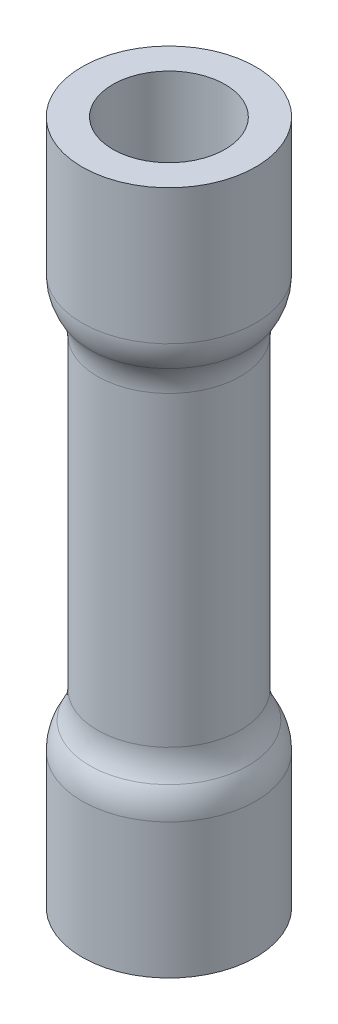
SolidWorks part; units mm, degrees
material "PVC 0.007 Plasticized"
ref_plane "Front Plane" through (0, 0, 0) normal (0, 0, 1) x (1, 0, 0)
ref_plane "Top Plane" through (0, 0, 0) normal (0, 1, 0) x (1, 0, 0)
ref_plane "Right Plane" through (0, 0, 0) normal (1, 0, 0) x (0, 0, -1)
sketch "Sketch1" plane through (0, 0, 0) normal (0, 0, 1) x (1, 0, 0)
  line L0 (1.778, 12.319) -> (1.778, 4.699)
  line L1 (2.159, 0) -> (2.159, 3.361)
  line L2 (0, 8.509) -> (2.159, 8.509) construction
  line L3 (2.159, 13.657) -> (2.159, 17.018)
  line L5 (0, 17.018) -> (0, 0) construction
  arc A0 (2.159, 3.361) -> (1.9685, 4.03) centre (0.889, 3.361) ccw
  arc A1 (1.9685, 4.03) -> (1.778, 4.699) centre (3.048, 4.699) cw
  arc A2 (2.159, 13.657) -> (1.9685, 12.988) centre (0.889, 13.657) cw
  arc A3 (1.9685, 12.988) -> (1.778, 12.319) centre (3.048, 12.319) ccw
  dimension "D5" = 1.27
  dimension "D1" = 17.018
  dimension "D2" = 2.159
  dimension "D3" = 0.381
  dimension "D4" = 7.62
revolve "Revolve-Thin1" add sketch "Sketch1" angle 360 about L5
